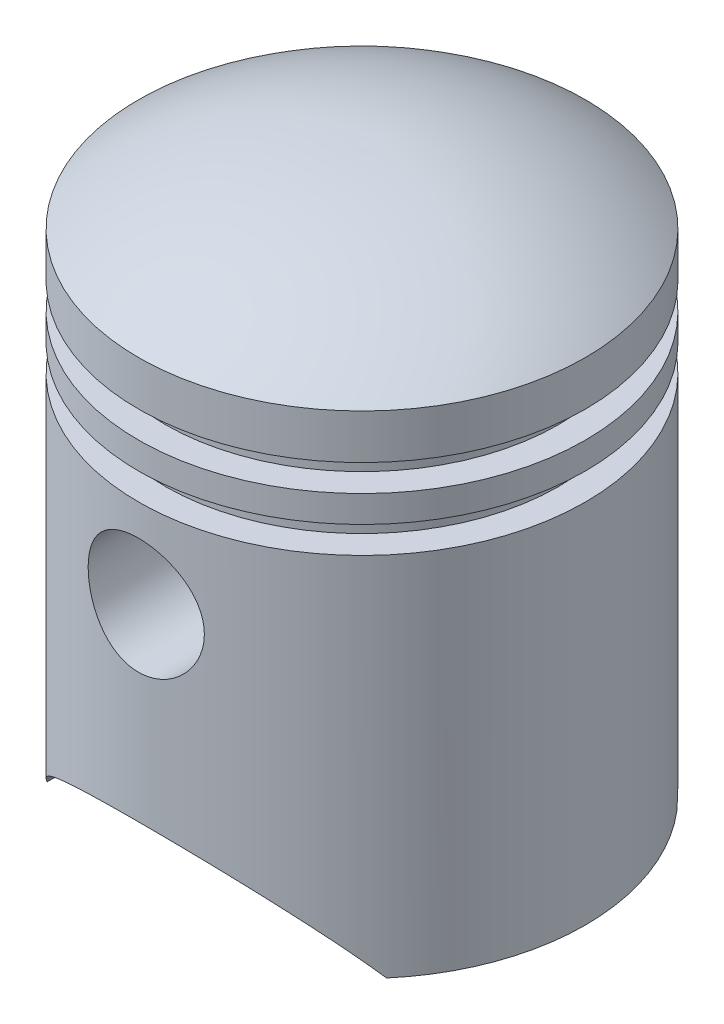
SolidWorks part; units mm, degrees
ref_plane "Front Plane" through (0, 0, 0) normal (0, 0, 1) x (1, 0, 0)
ref_plane "Top Plane" through (0, 0, 0) normal (0, 1, 0) x (1, 0, 0)
ref_plane "Right Plane" through (0, 0, 0) normal (1, 0, 0) x (0, 0, -1)
sketch "Sketch1" plane through (0, 0, 0) normal (0, 0, 1) x (1, 0, 0)
  line L0 (0, -31.5) -> (0, 31.5) construction
  line L1 (-23, -31.5) -> (-23, 7.5)
  line L2 (-25, -31.5) -> (-25, 9.5)
  line L3 (-25, 9.5) -> (-22, 9.5)
  line L4 (-22, 9.5) -> (-22, 12.5)
  line L5 (-22, 12.5) -> (-25, 12.5)
  line L6 (-25, 12.5) -> (-25, 15.5)
  line L7 (-25, 15.5) -> (-22, 15.5)
  line L8 (-22, 15.5) -> (-22, 18.5)
  line L9 (-22, 18.5) -> (-25, 18.5)
  line L10 (-25, 18.5) -> (-25, 23.5)
  line L11 (-23, 7.5) -> (-20, 7.5)
  line L12 (-20, 7.5) -> (-20, 20.5)
  line L13 (0, 31.5) -> (0, 29.5006)
  line L14 (0, 29.5006) -> (-0.0492, 29.5006)
  line L17 (-20, 20.5) -> (-23, 20.5)
  line L18 (-23, 20.5) -> (-23, 22.4845)
  line L19 (-23, -31.5) -> (-25, -31.5)
  line L21 (-20, 7.5) -> (-20, 14) construction
  line L22 (-20, 14) -> (-20, 20.5) construction
  line L23 (-20, 14) -> (-20, 14) construction
  line L24 (-20, 14) -> (-20, 14) construction
  line L25 (-20, 14) -> (-20, 14) construction
  arc A1 (-25, 23.5) -> (0, 31.5) centre (-0.9839, -8.4879) cw
  arc A2 (-23, 22.4845) -> (-0.0492, 29.5006) centre (-0.9839, -8.4879) cw
  point P4 (0, 0)
  dimension "D1" = 25
  dimension "D8" = 40
  dimension "D2" = 25
  dimension "D3" = 63
  dimension "D4" = 5
  dimension "D5" = 3
  dimension "D6" = 3
  dimension "D7" = 55
  dimension "D10" = 1.9994
  dimension "D9" = 2
revolve "Revolve9" add sketch "Sketch1" angle 360 about L0
sketch "Sketch2" plane through (0, 0, 0) normal (0, 0, 1) x (1, 0, 0)
  line L0 (-19, -31.5) -> (19, -31.5)
  line L2 (-25, -31.5) -> (25, -31.5)
  line L3 (0, -31.5) -> (0, -21.5)
  circle A0 centre (0, -0.5) radius 6.5
  arc A2 (19, -31.5) -> (-19, -31.5) centre (0, -44.55) ccw
  dimension "D1" = 13
  dimension "D3" = 38
  dimension "D2" = 32
  dimension "D4" = 10
extrude "Cut-Extrude2" cut sketch "Sketch2" against normal through all both and the other way through all contours A0 | L0 A2
sketch "Sketch3" plane through (0, 0, 0) normal (0, 0, 1) x (1, 0, 0)
  circle A0 centre (0, -0.5) radius 6.5
  circle A1 centre (0, -0.5) radius 7.5
  dimension "D1" = 13
  dimension "D2" = 15
extrude "Boss-Extrude1" add sketch "Sketch3" along normal up to next from offset 12
mirror "Mirror1" about plane through (0, 0, 0) normal (0, 0, 1) of "Boss-Extrude1"
